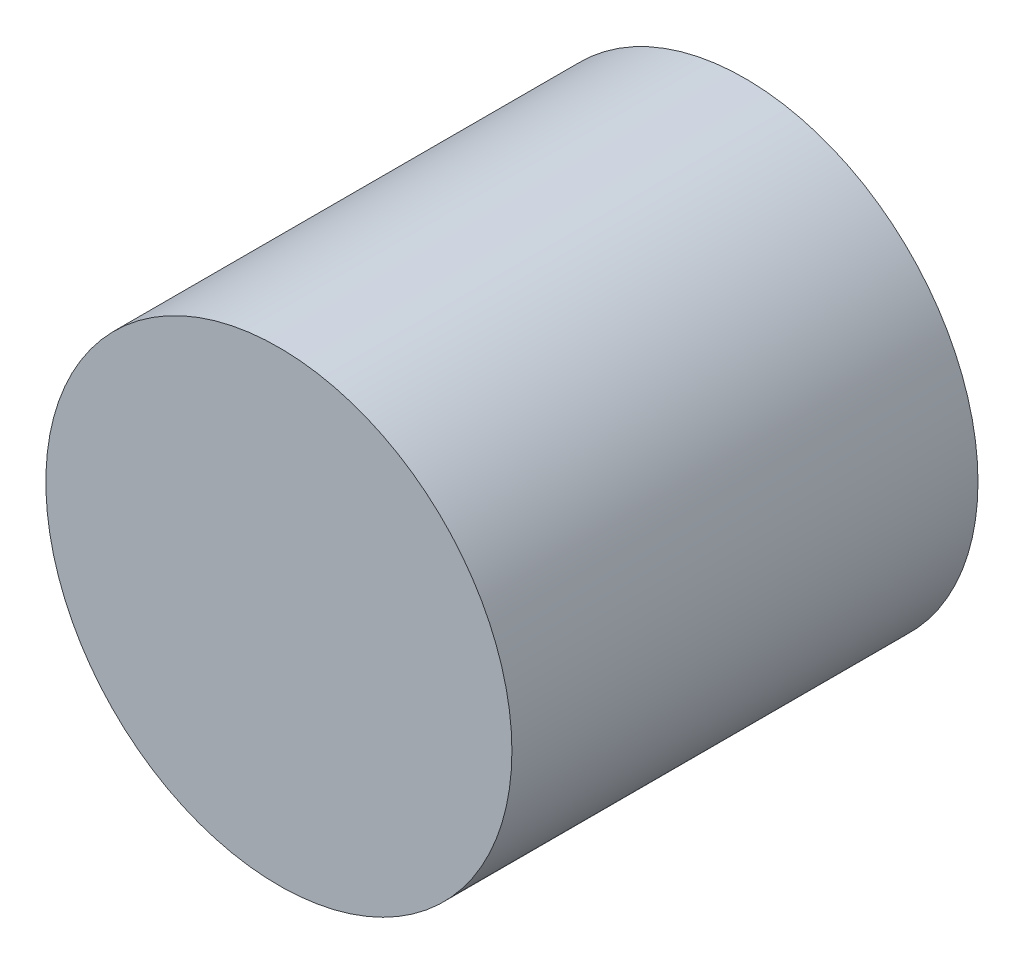
SolidWorks part; units mm, degrees
ref_plane "Płaszczyzna przednia" through (0, 0, 0) normal (0, 0, 1) x (1, 0, 0)
ref_plane "Płaszczyzna górna" through (0, 0, 0) normal (0, 1, 0) x (1, 0, 0)
ref_plane "Płaszczyzna prawa" through (0, 0, 0) normal (1, 0, 0) x (0, 0, -1)
sketch "Szkic1" plane through (0, 0, 0) normal (0, 0, 1) x (1, 0, 0)
  circle A0 centre (0, 0) radius 5
  dimension "D1" = 10
extrude "Dodanie-wyciągnięcie1" add sketch "Szkic1" along normal blind 10
